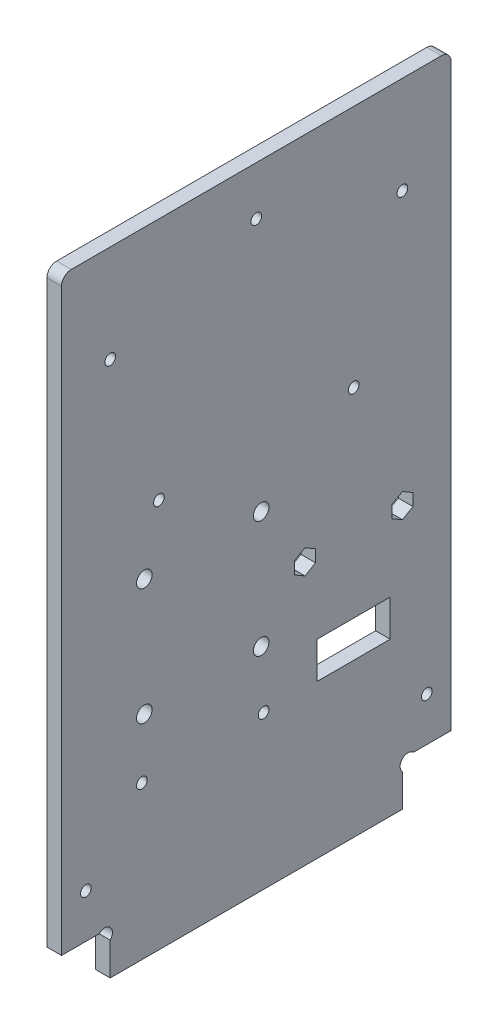
SolidWorks part; units mm, degrees
ref_plane "Plan de face" through (0, 0, 0) normal (0, 0, 1) x (1, 0, 0)
ref_plane "Plan de dessus" through (0, 0, 0) normal (0, 1, 0) x (1, 0, 0)
ref_plane "Plan de droite" through (0, 0, 0) normal (1, 0, 0) x (0, 0, -1)
sketch "Esquisse1" plane through (0, 0, 0) normal (1, 0, 0) x (0, 0, -1)
  line L8 (10, 6.7373) -> (10, 0)
  line L9 (70, 6.7373) -> (70, 0)
  line L10 (7.7373, 9) -> (0, 9)
  line L11 (10, 0) -> (70, 0)
  line L12 (72.2627, 9) -> (80, 9)
  line L13 (0, 9) -> (0, 130)
  line L14 (0, 130) -> (80, 130)
  line L15 (80, 130) -> (80, 9)
  arc A0 (10, 6.7373) -> (7.7373, 9) centre (8.8686, 7.8686) ccw
  arc A1 (70, 6.7373) -> (72.2627, 9) centre (71.1314, 7.8686) cw
  dimension "D7" = 1.1314
  dimension "D6" = 1.6
  dimension "D1" = 9
  dimension "D2" = 10
  dimension "D3" = 10
  dimension "D4" = 80
  dimension "D5" = 130
  dimension "D8" = 1.1314
  dimension "D9" = 1.1314
  dimension "D10" = 1.1314
extrude "Extrusion1" add sketch "Esquisse1" along normal blind 3
sketch "Esquisse2" plane through (3, 0, 0) normal (1, 0, 0) x (0, 0, -1)
  line L0 (0, 9) -> (7.7373, 9) construction
  line L1 (0, 130) -> (0, 9) construction
  line L2 (80, 9) -> (80, 130) construction
  line L3 (72.2627, 9) -> (80, 9) construction
  line L4 (80, 130) -> (0, 130) construction
  circle A0 centre (60, 80) radius 1.1
  circle A1 centre (10, 110) radius 1.1
  circle A2 centre (20, 80) radius 1.1
  circle A3 centre (70, 110) radius 1.1
  circle A4 centre (17, 67.45) radius 1.6
  circle A5 centre (17, 43.45) radius 1.6
  circle A6 centre (41, 43.45) radius 1.6
  circle A7 centre (41, 67.45) radius 1.6
  circle A8 centre (40, 120) radius 1.1
  circle A9 centre (70, 54) radius 1.1
  circle A10 centre (50, 54) radius 1.1
  dimension "D5" = 17
  dimension "D7" = 10
  dimension "D9" = 10
  dimension "D4" = 3.2
  dimension "D6" = 2.2
  dimension "D1" = 58.45
  dimension "D2" = 24
  dimension "D3" = 24
  dimension "D8" = 40
  dimension "D10" = 30
  dimension "D11" = 10
  dimension "D12" = 20
  dimension "D13" = 10
  dimension "D14" = 10
  dimension "D15" = 10
  dimension "D16" = 20
  dimension "D17" = 45
extrude "Enlèv. mat.-Extru.1" cut sketch "Esquisse2" against normal through all
sketch "Esquisse3" plane through (0, 0, 0) normal (-1, 0, 0) x (0, 0, 1)
  line L1 (-67.5, 39) -> (-52.5, 39)
  line L2 (-67.5, 39) -> (-67.5, 31.5)
  line L3 (-67.5, 31.5) -> (-52.5, 31.5)
  line L4 (-52.5, 39) -> (-52.5, 31.5)
  circle A0 centre (-70, 54) radius 1.1 construction
  circle A1 centre (-50, 54) radius 1.1 construction
  dimension "D4" = 2.5
  dimension "D1" = 15
  dimension "D2" = 7.5
  dimension "D3" = 15
  dimension "D5" = 2.5
extrude "Enlèv. mat.-Extru.2" cut sketch "Esquisse3" against normal through all
sketch "Esquisse4" plane through (3, 0, 0) normal (1, 0, 0) x (0, 0, -1)
  line L3 (0, 9) -> (7.7373, 9) construction
  line L4 (0, 130) -> (0, 9) construction
  line L5 (80, 9) -> (80, 130) construction
  circle A2 centre (75, 18) radius 1.1
  circle A3 centre (5, 18) radius 1.1
  dimension "D1" = 2.2
  dimension "D2" = 5
  dimension "D3" = 5
  dimension "D5" = 9
extrude "Enlèv. mat.-Extru.3" cut sketch "Esquisse4" against normal through all
sketch "Esquisse5" plane through (3, 0, 0) normal (1, 0, 0) x (0, 0, -1)
  line L0 (80, 9) -> (80, 130) construction
  line L1 (50, 51.5) -> (52.1651, 52.75)
  line L2 (52.1651, 52.75) -> (52.1651, 55.25)
  line L3 (52.1651, 55.25) -> (50, 56.5)
  line L4 (50, 56.5) -> (47.8349, 55.25)
  line L5 (47.8349, 55.25) -> (47.8349, 52.75)
  line L6 (47.8349, 52.75) -> (50, 51.5)
  line L7 (70, 51.5) -> (72.1651, 52.75)
  line L8 (72.1651, 52.75) -> (72.1651, 55.25)
  line L9 (72.1651, 55.25) -> (70, 56.5)
  line L10 (70, 56.5) -> (67.8349, 55.25)
  line L11 (67.8349, 55.25) -> (67.8349, 52.75)
  line L12 (67.8349, 52.75) -> (70, 51.5)
  circle A0 centre (50, 54) radius 2.1651 construction
  circle A1 centre (70, 54) radius 2.1651 construction
  dimension "D1" = 2.5
  dimension "D2" = 2.5
extrude "Enlèv. mat.-Extru.4" cut sketch "Esquisse5" against normal through all
fillet "Congé1" radius 2 2 edges at (1.5, 130, -80) (1.5, 130, 0)
sketch "Esquisse6" plane through (3, 0, 0) normal (1, 0, 0) x (0, 0, -1)
  line L0 (17, 43.45) -> (17, 35.9367) construction
  line L1 (41, 43.45) -> (41, 36.8364) construction
  circle A0 centre (16.5, 31.4604) radius 1.1
  circle A1 centre (41.5, 31.4604) radius 1.1
  point P4 (0, 0)
  point P5 (0, 0)
  point P6 (0, 0)
  point P13 (0, 0)
  point P14 (14.5062, 31.712)
  point P15 (41, 31.4503)
  point P16 (0, 0)
  point P17 (17, 31.4604)
  dimension "D1" = 2.2
  dimension "D4" = 24
  dimension "D2" = 0.5
  dimension "D3" = 12
  dimension "D5" = 0.5
extrude "Enlèv. mat.-Extru.5" cut sketch "Esquisse6" against normal through all
